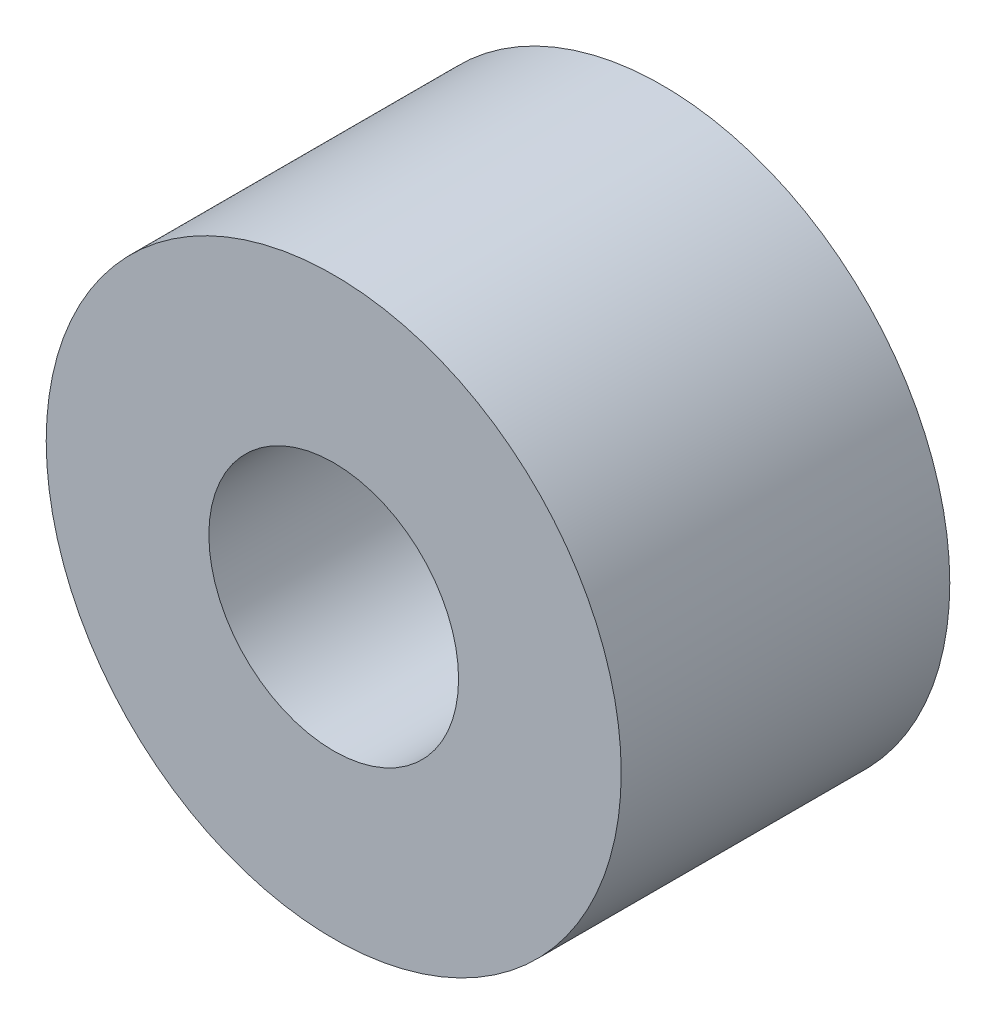
SolidWorks part; units mm, degrees
ref_plane "Front Plane" through (0, 0, 0) normal (0, 0, 1) x (1, 0, 0)
ref_plane "Top Plane" through (0, 0, 0) normal (0, 1, 0) x (1, 0, 0)
ref_plane "Right Plane" through (0, 0, 0) normal (1, 0, 0) x (0, 0, -1)
sketch "Sketch1" plane through (0, 0, 0) normal (0, 0, 1) x (1, 0, 0)
  circle A0 centre (0, 0) radius 5.5562
  dimension "D1" = 11.1125
extrude "Extrude1" add sketch "Sketch1" along normal mid plane 6.35
sketch "Sketch2" plane through (0, 0, 3.175) normal (0, 0, 1) x (1, 0, 0)
  circle A0 centre (0, 0) radius 2.413
  dimension "D1" = 4.826
extrude "Extrude2" cut sketch "Sketch2" against normal through all
